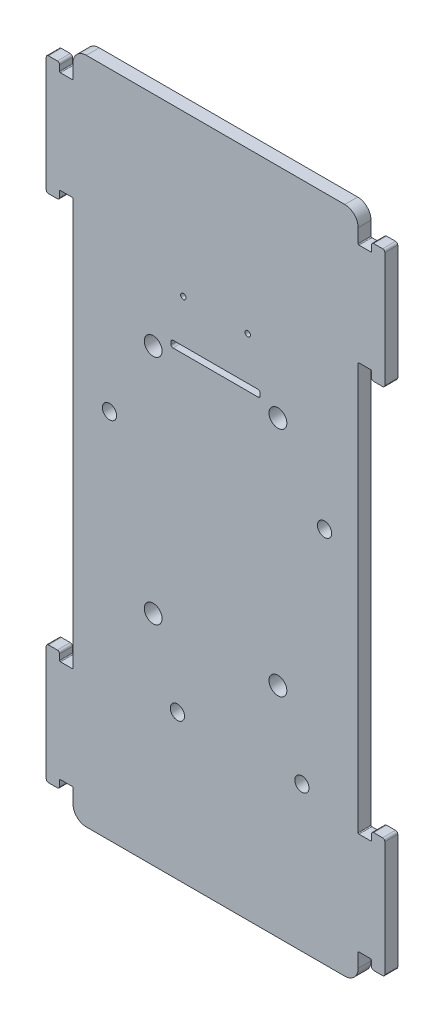
SolidWorks part; units mm, degrees
material "普通碳钢"
ref_plane "前视基准面" through (0, 0, 0) normal (0, 0, 1) x (1, 0, 0)
ref_plane "上视基准面" through (0, 0, 0) normal (0, 1, 0) x (1, 0, 0)
ref_plane "右视基准面" through (0, 0, 0) normal (1, 0, 0) x (0, 0, -1)
sketch "草图1" plane through (0, 0, 0) normal (0, 0, 1) x (1, 0, 0)
  line L0 (32.2, 68.7) -> (34.8, 68.7)
  line L1 (-29, 75) -> (29, 75)
  line L2 (-32, 72) -> (-32, -72) construction
  line L3 (-29, -75) -> (29, -75)
  line L4 (32, 72) -> (32, -72) construction
  line L5 (-32, 75) -> (32, -75) construction
  line L6 (-32, -75) -> (32, 75) construction
  line L7 (35, 68.9) -> (35, 70.15)
  line L8 (35.5, 70.65) -> (37.5, 70.65)
  line L9 (38, 70.15) -> (38, 44.35)
  line L10 (37.5, 43.85) -> (35.5, 43.85)
  line L11 (35, 44.35) -> (35, 45.6)
  line L12 (34.8, 45.8) -> (32.2, 45.8)
  line L13 (38, 57.25) -> (32, 57.25) construction
  line L14 (32, 68.9) -> (32, 72)
  line L15 (32, 45.6) -> (32, -45.6)
  line L16 (0, 0) -> (19.5271, 0) construction
  line L17 (0, 0) -> (0, 19.9471) construction
  line L18 (34.8, -45.8) -> (32.2, -45.8)
  line L19 (35, -44.35) -> (35, -45.6)
  line L20 (37.5, -43.85) -> (35.5, -43.85)
  line L21 (32, -68.9) -> (32, -72)
  line L22 (32.2, -68.7) -> (34.8, -68.7)
  line L23 (35, -68.9) -> (35, -70.15)
  line L24 (35.5, -70.65) -> (37.5, -70.65)
  line L25 (38, -70.15) -> (38, -44.35)
  line L26 (-37.5, 43.85) -> (-35.5, 43.85)
  line L27 (-35, 44.35) -> (-35, 45.6)
  line L28 (-34.8, 45.8) -> (-32.2, 45.8)
  line L29 (-32, 45.6) -> (-32, -45.6)
  line L30 (-34.8, -45.8) -> (-32.2, -45.8)
  line L31 (-35, -44.35) -> (-35, -45.6)
  line L32 (-37.5, -43.85) -> (-35.5, -43.85)
  line L33 (-38, -70.15) -> (-38, -44.35)
  line L34 (-35.5, -70.65) -> (-37.5, -70.65)
  line L35 (-35, -68.9) -> (-35, -70.15)
  line L36 (-32.2, -68.7) -> (-34.8, -68.7)
  line L37 (-32, -68.9) -> (-32, -72)
  line L38 (-37.5, 43.85) -> (-35.5, 43.85)
  line L39 (-32, 68.9) -> (-32, 72)
  line L40 (-32.2, 68.7) -> (-34.8, 68.7)
  line L41 (-35, 68.9) -> (-35, 70.15)
  line L42 (-35.5, 70.65) -> (-37.5, 70.65)
  line L43 (-38, 70.15) -> (-38, 44.35)
  arc A0 (-32, -72) -> (-29, -75) centre (-29, -72) ccw
  arc A1 (29, -75) -> (32, -72) centre (29, -72) ccw
  arc A2 (29, 75) -> (32, 72) centre (29, 72) cw
  arc A3 (-32, 72) -> (-29, 75) centre (-29, 72) cw
  arc A4 (35, 70.15) -> (35.5, 70.65) centre (35.5, 70.15) cw
  arc A5 (35, 44.35) -> (35.5, 43.85) centre (35.5, 44.35) ccw
  arc A6 (37.5, 43.85) -> (38, 44.35) centre (37.5, 44.35) ccw
  arc A7 (37.5, 70.65) -> (38, 70.15) centre (37.5, 70.15) cw
  arc A8 (37.5, 43.85) -> (38, 44.35) centre (37.5, 44.35) ccw
  arc A9 (34.8, 45.8) -> (35, 45.6) centre (34.8, 45.6) cw
  arc A10 (34.8, 68.7) -> (35, 68.9) centre (34.8, 68.9) ccw
  arc A11 (32, 45.6) -> (32.2, 45.8) centre (32.2, 45.6) cw
  arc A12 (32, 68.9) -> (32.2, 68.7) centre (32.2, 68.9) ccw
  arc A13 (32, -45.6) -> (32.2, -45.8) centre (32.2, -45.6) ccw
  arc A14 (34.8, -45.8) -> (35, -45.6) centre (34.8, -45.6) ccw
  arc A15 (35, -44.35) -> (35.5, -43.85) centre (35.5, -44.35) cw
  arc A16 (32, -68.9) -> (32.2, -68.7) centre (32.2, -68.9) cw
  arc A17 (34.8, -68.7) -> (35, -68.9) centre (34.8, -68.9) cw
  arc A18 (35, -70.15) -> (35.5, -70.65) centre (35.5, -70.15) ccw
  arc A19 (37.5, -70.65) -> (38, -70.15) centre (37.5, -70.15) ccw
  arc A20 (37.5, -43.85) -> (38, -44.35) centre (37.5, -44.35) cw
  arc A21 (-35, 44.35) -> (-35.5, 43.85) centre (-35.5, 44.35) cw
  arc A22 (-34.8, 45.8) -> (-35, 45.6) centre (-34.8, 45.6) ccw
  arc A23 (-32, 45.6) -> (-32.2, 45.8) centre (-32.2, 45.6) ccw
  arc A24 (-32, -45.6) -> (-32.2, -45.8) centre (-32.2, -45.6) cw
  arc A25 (-34.8, -45.8) -> (-35, -45.6) centre (-34.8, -45.6) cw
  arc A26 (-35, -44.35) -> (-35.5, -43.85) centre (-35.5, -44.35) ccw
  arc A27 (-37.5, -43.85) -> (-38, -44.35) centre (-37.5, -44.35) ccw
  arc A28 (-37.5, -70.65) -> (-38, -70.15) centre (-37.5, -70.15) cw
  arc A29 (-35, -70.15) -> (-35.5, -70.65) centre (-35.5, -70.15) cw
  arc A30 (-34.8, -68.7) -> (-35, -68.9) centre (-34.8, -68.9) ccw
  arc A31 (-32, -68.9) -> (-32.2, -68.7) centre (-32.2, -68.9) ccw
  arc A32 (-37.5, 43.85) -> (-38, 44.35) centre (-37.5, 44.35) cw
  arc A33 (-32, 68.9) -> (-32.2, 68.7) centre (-32.2, 68.9) cw
  arc A34 (-34.8, 68.7) -> (-35, 68.9) centre (-34.8, 68.9) cw
  arc A35 (-35, 70.15) -> (-35.5, 70.65) centre (-35.5, 70.15) ccw
  arc A36 (-37.5, 70.65) -> (-38, 70.15) centre (-37.5, 70.15) ccw
  point P0 (0, 0)
  point P33 (35, 69.525)
  point P45 (32, 45.8)
  point P53 (32, 68.7)
  point P75 (32, 0)
  point P77 (38, -57.25)
  dimension "D3" = 3
  dimension "D6" = 0.2
  dimension "D7" = 0.5
  dimension "D8" = 0.2
  dimension "D11" = 0.2
  dimension "D1" = 64
  dimension "D2" = 150
  dimension "D4" = 22.9
  dimension "D5" = 26.8
  dimension "D9" = 3
  dimension "D10" = 3
  dimension "D12" = 114.5
extrude "凸台-拉伸1" add sketch "草图1" along normal mid plane 2.9 contours L42 A36 L43 A32 L26 A21 L27 A22 L28 A23 L29 A24 L30 A25 L31 A26 L32 A27 L33 A28 L34 A29 L35 A30 L36 A31 L37 A0 L3 A1 L21 A16 L22 A17 L23 A18 L24 A19 L25 A20 L20 A15 L19 A14 L18 A13 L15 A11 L12 A9 L11
sketch "草图2" plane through (0, 0, -1.45) normal (0, 0, -1) x (-1, 0, 0)
  circle A0 centre (23.8, 8.34) radius 1.6
  circle A1 centre (8.56, -42.46) radius 1.6
  circle A2 centre (-19.38, -42.46) radius 1.6
  circle A3 centre (-24.46, 9.61) radius 1.6
  dimension "D1" = 3.2
  dimension "D2" = 3.2
  dimension "D3" = 3.2
  dimension "D4" = 3.2
extrude "切除-拉伸1" cut sketch "草图2" against normal up to next
sketch "草图3" plane through (0, 0, 1.45) normal (0, 0, 1) x (1, 0, 0)
  line L0 (0, 0) -> (11.2992, 0) construction
  line L1 (-14, 26) -> (14, 26) construction
  line L2 (-14, 26) -> (-14, -26) construction
  line L3 (-14, -26) -> (14, -26) construction
  line L4 (14, 26) -> (14, -26) construction
  line L5 (-14, 26) -> (14, -26) construction
  line L6 (-14, -26) -> (14, 26) construction
  line L7 (0, 0) -> (0, -11.627) construction
  circle A0 centre (14, 26) radius 2
  circle A1 centre (14, -26) radius 2
  circle A2 centre (-14, 26) radius 2
  circle A3 centre (-14, -26) radius 2
  point P0 (0, 0)
  dimension "D3" = 4
  dimension "D1" = 28
  dimension "D2" = 52
extrude "切除-拉伸2" cut sketch "草图3" against normal blind 10
sketch "草图4" plane through (0, 0, 1.45) normal (0, 0, 1) x (1, 0, 0)
  line L0 (0, 75) -> (0, 56.5541) construction
  line L1 (-29, 75) -> (29, 75) construction
  line L2 (0, 56.5541) -> (0, 28.59) construction
  line L3 (-9.55, 29.34) -> (9.55, 29.34)
  line L4 (-10, 28.89) -> (-10, 28.29)
  line L5 (-9.55, 27.84) -> (9.55, 27.84)
  line L6 (10, 28.89) -> (10, 28.29)
  line L7 (-10, 29.34) -> (10, 27.84) construction
  line L8 (-10, 27.84) -> (10, 29.34) construction
  circle A0 centre (-7.23, 39) radius 0.6
  circle A1 centre (7.23, 39) radius 0.6
  arc A2 (9.55, 29.34) -> (10, 28.89) centre (9.55, 28.89) cw
  arc A3 (10, 28.29) -> (9.55, 27.84) centre (9.55, 28.29) cw
  arc A4 (-9.55, 27.84) -> (-10, 28.29) centre (-9.55, 28.29) cw
  arc A5 (-10, 28.89) -> (-9.55, 29.34) centre (-9.55, 28.89) cw
  point P9 (0, 28.59)
  dimension "D2" = 1.2
  dimension "D7" = 0.45
  dimension "D1" = 14.46
  dimension "D3" = 36
  dimension "D4" = 10.41
  dimension "D5" = 20
  dimension "D6" = 1.5
extrude "切除-拉伸3" cut sketch "草图4" against normal blind 10
